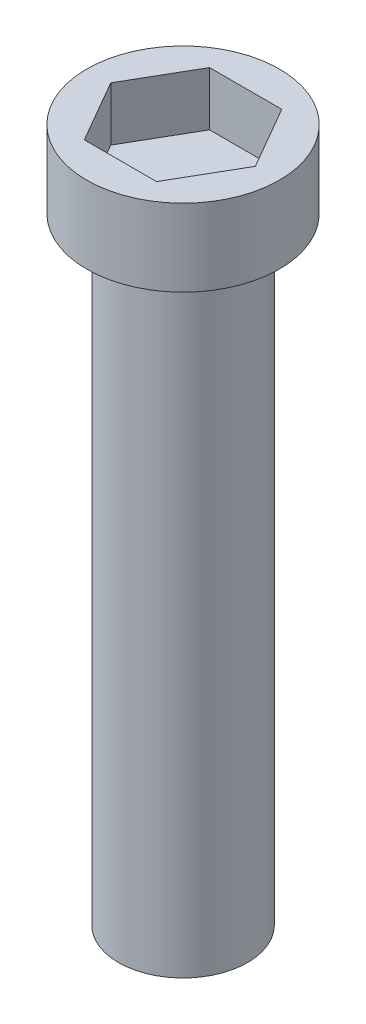
SolidWorks part; units mm, degrees
material "201 Acero inoxidable recocido (SS)"
ref_plane "Alzado" through (0, 0, 0) normal (0, 0, 1) x (1, 0, 0)
ref_plane "Planta" through (0, 0, 0) normal (0, 1, 0) x (1, 0, 0)
ref_plane "Vista lateral" through (0, 0, 0) normal (1, 0, 0) x (0, 0, -1)
sketch "Croquis1" plane through (0, 0, 0) normal (0, 1, 0) x (1, 0, 0)
  circle A0 centre (0, 0) radius 5
  dimension "D1" = 10
extrude "Saliente-Extruir1" add sketch "Croquis1" along normal blind 4
sketch "Croquis2" plane through (0, 0, 0) normal (0, 1, 0) x (1, 0, 0)
  circle A0 centre (0, 0) radius 3.35
  dimension "D1" = 6.7
extrude "Saliente-Extruir2" add sketch "Croquis2" against normal blind 32
ref_plane "Plano1" through (0, 3.7, 0) normal (0, 1, 0) x (1, 0, 0)
sketch "Croquis4" plane through (0, 3.7, 0) normal (0, 1, 0) x (1, 0, 0)
  line L1 (3.7528, 0) -> (1.8764, 3.25)
  line L2 (1.8764, 3.25) -> (-1.8764, 3.25)
  line L3 (-1.8764, 3.25) -> (-3.7528, 0)
  line L4 (-3.7528, 0) -> (-1.8764, -3.25)
  line L5 (-1.8764, -3.25) -> (1.8764, -3.25)
  line L6 (1.8764, -3.25) -> (3.7528, 0)
  circle A0 centre (0, 0) radius 3.25 construction
  dimension "D1" = 6.5
extrude "Cortar-Extruir1" cut sketch "Croquis4" against normal blind 2.5 and the other way through all
